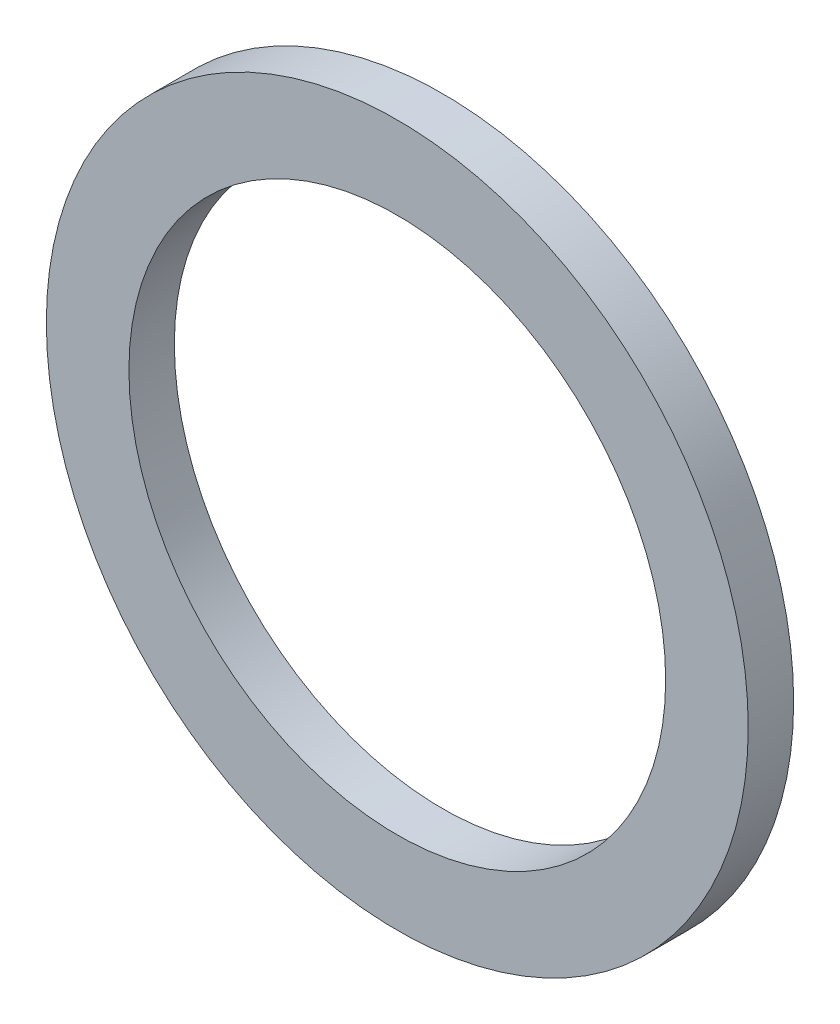
SolidWorks part; units mm, degrees
material "PTFE (general)"
ref_plane "Front Plane" through (0, 0, 0) normal (0, 0, 1) x (1, 0, 0)
ref_plane "Top Plane" through (0, 0, 0) normal (0, 1, 0) x (1, 0, 0)
ref_plane "Right Plane" through (0, 0, 0) normal (1, 0, 0) x (0, 0, -1)
sketch "Sketch1" plane through (0, 0, 0) normal (0, 0, 1) x (1, 0, 0)
  circle A0 centre (0, 0) radius 3.302
  circle A1 centre (0, 0) radius 4.318
  dimension "ID" = 6.604
  dimension "OD" = 8.636
extrude "Extrude1" add sketch "Sketch1" against normal blind 0.5588
